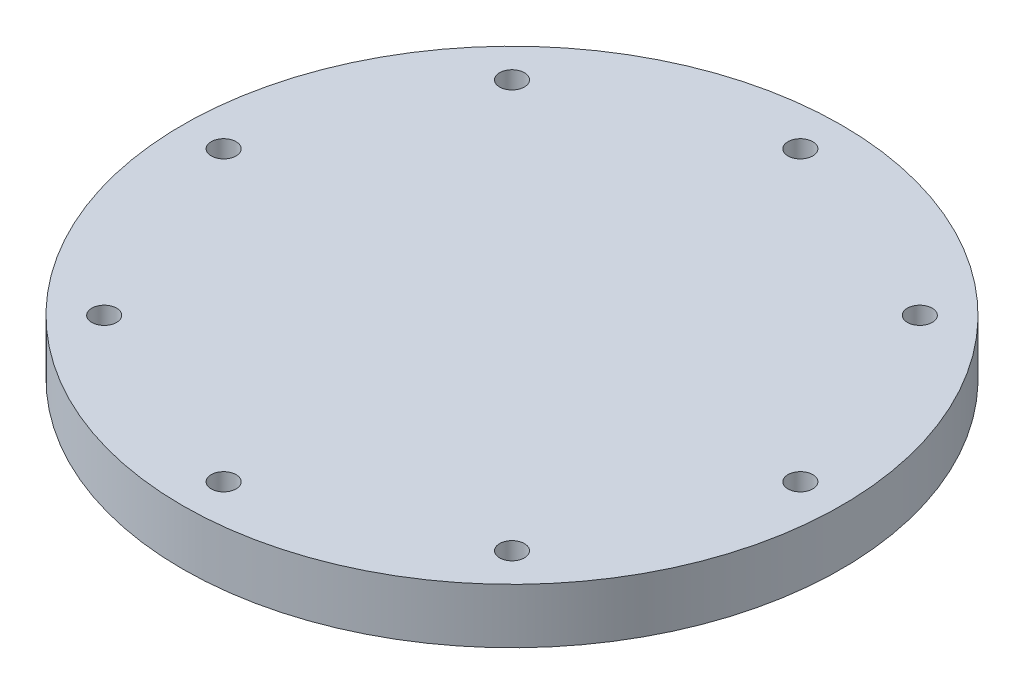
SolidWorks part; units mm, degrees
ref_plane "Front Plane" through (0, 0, 0) normal (0, 0, 1) x (1, 0, 0)
ref_plane "Top Plane" through (0, 0, 0) normal (0, 1, 0) x (1, 0, 0)
ref_plane "Right Plane" through (0, 0, 0) normal (1, 0, 0) x (0, 0, -1)
sketch "Sketch1" plane through (0, 0, 0) normal (0, 1, 0) x (1, 0, 0)
  circle A0 centre (0, 0) radius 38.1
  dimension "D1" = 76.2
extrude "Boss-Extrude1" add sketch "Sketch1" along normal blind 6.35
sketch "Sketch2" plane through (0, 0, 0) normal (0, -1, 0) x (1, 0, 0)
  circle A0 centre (0, 0) radius 33.3375
  circle A1 centre (0, 33.3375) radius 0.762
  dimension "D1" = 66.675
hole_wizard "CBORE for #4 Button Head Cap Screw1" positions "Sketch5" profile "Sketch4" counterbore size "#4" standard "ANSI Inch" end condition through all
sketch "Sketch5" plane through (0, 0, 0) normal (0, -1, 0) x (-1, 0, 0)
  point P0 (0, -33.3375)
sketch "Sketch4" plane through (0, 0, 33.3375) normal (1, 0, 0) x (0, 0, -1)
  line L0 (0, 0) -> (0, 6.35)
  line L1 (0, 6.35) -> (1.4351, 6.35)
  line L3 (1.4351, 6.35) -> (1.4351, 1.905)
  line L4 (1.4351, 1.905) -> (2.413, 1.905)
  line L5 (2.413, 1.905) -> (2.413, 0)
  line L7 (2.413, 0) -> (0, 0)
  line L11 (0, -6.35) -> (0, 107.95) construction
  dimension "Thru Hole Dia." = 2.8702
  dimension "Thru Hole Depth" = 6.35
  dimension "C'Bore Dia." = 4.826
  dimension "C'Bore Depth" = 1.905
pattern_circular "CirPattern1" count 8 over 360 about axis through (0, 0, 0) along (0, 1, 0) of "CBORE for #4 Button Head Cap Screw1"
sketch "Sketch6" plane through (0, 6.35, 0) normal (0, 1, 0) x (1, 0, 0)
  circle A0 centre (0, 4.0796) radius 0.5592
